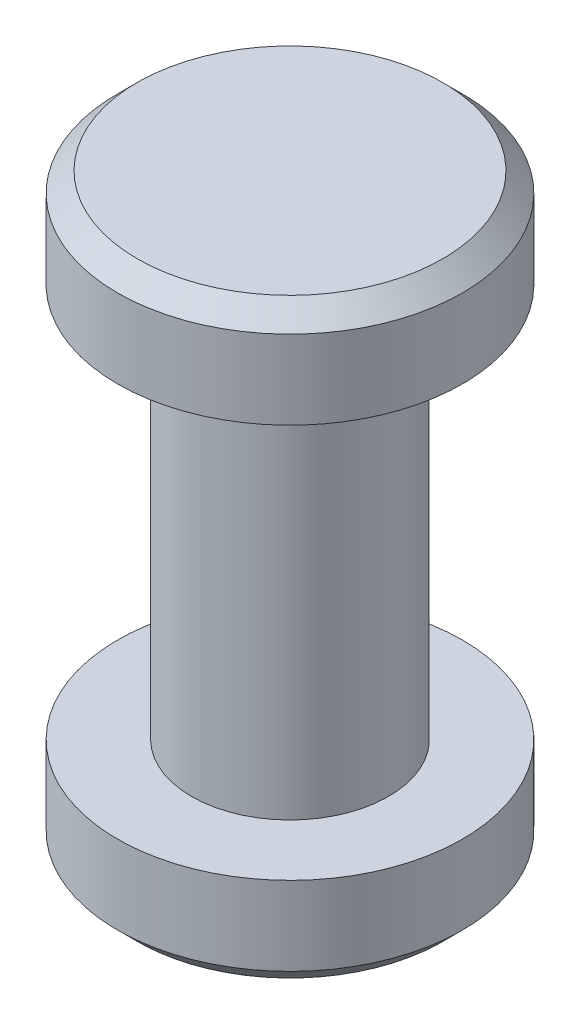
SolidWorks part; units mm, degrees
ref_plane "Front Plane" through (0, 0, 0) normal (0, 0, 1) x (1, 0, 0)
ref_plane "Top Plane" through (0, 0, 0) normal (0, 1, 0) x (1, 0, 0)
ref_plane "Right Plane" through (0, 0, 0) normal (1, 0, 0) x (0, 0, -1)
sketch "Sketch1" plane through (0, 0, 0) normal (0, 1, 0) x (1, 0, 0)
  circle A0 centre (0, 0) radius 1
  dimension "D1" = 2
extrude "Boss-Extrude1" add sketch "Sketch1" along normal blind 4
sketch "Sketch2" plane through (0, 4, 0) normal (0, 1, 0) x (1, 0, 0)
  circle A0 centre (0, 0) radius 1.75
  dimension "D1" = 3.5
extrude "Boss-Extrude2" add sketch "Sketch2" along normal blind 1
chamfer "Chamfer1" distance 0.2 angle 45 1 edges at (0, 5, 1.75)
sketch "Sketch3" plane through (0, 0, 0) normal (0, -1, 0) x (1, 0, 0)
  circle A0 centre (0, 0) radius 1.75
  dimension "D1" = 3.5
extrude "Boss-Extrude3" add sketch "Sketch3" along normal blind 1
chamfer "Chamfer2" distance 0.2 angle 45 1 edges at (0, -1, -1.75)
